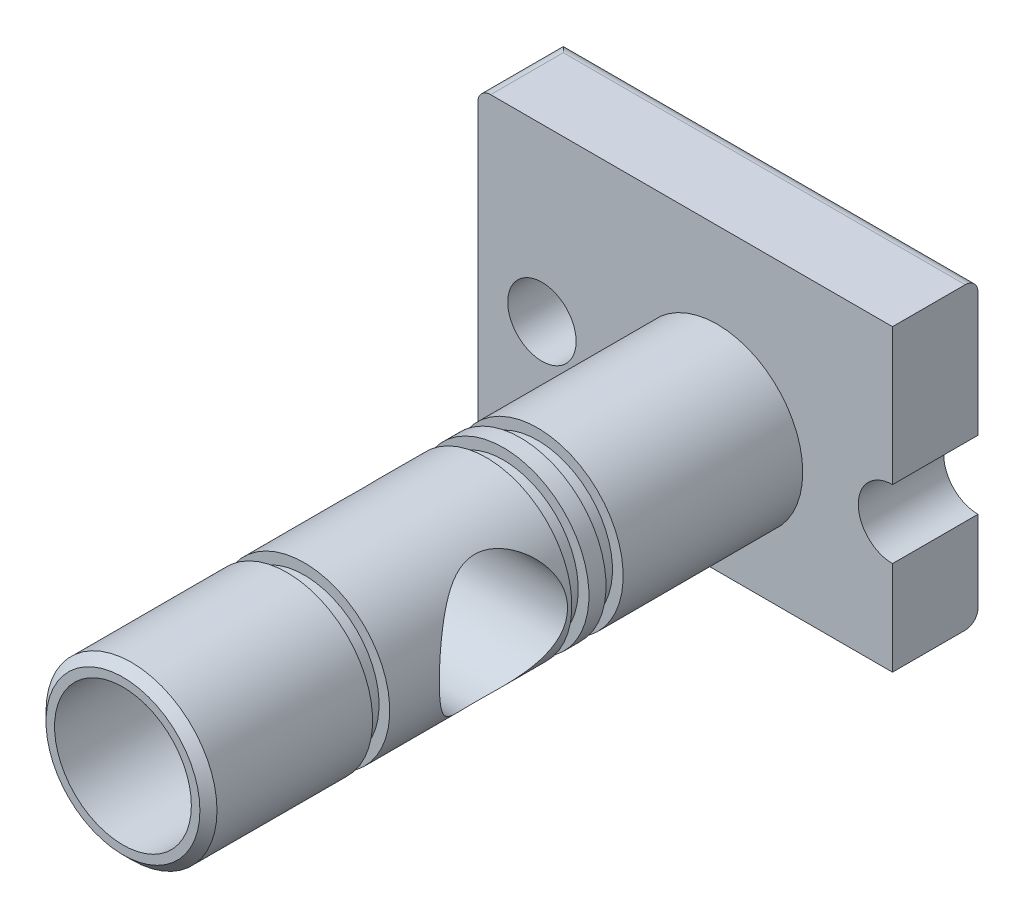
SolidWorks part; units mm, degrees
ref_plane "Front Plane" through (0, 0, 0) normal (0, 0, 1) x (1, 0, 0)
ref_plane "Top Plane" through (0, 0, 0) normal (0, 1, 0) x (1, 0, 0)
ref_plane "Right Plane" through (0, 0, 0) normal (1, 0, 0) x (0, 0, -1)
sketch "Sketch1" plane through (0, 0, 0) normal (0, 0, 1) x (1, 0, 0)
  line L1 (-56, 40) -> (41, 40)
  line L3 (-56, -30) -> (41, -30)
  line L4 (41, 40) -> (41, 8)
  line L5 (41, -8) -> (41, -30)
  line L6 (-56, 40) -> (-56, -30)
  arc A1 (41, 8) -> (41, -8) centre (41, 0) ccw
  circle A2 centre (-41, 0) radius 8
  dimension "D5" = 56
  dimension "D6" = 16
  dimension "D1" = 70
  dimension "D2" = 97
  dimension "D3" = 15
  dimension "D4" = 30
extrude "Boss-Extrude1" add sketch "Sketch1" along normal blind 20
sketch "Sketch2" plane through (0, 0, 20) normal (0, 0, 1) x (1, 0, 0)
  circle A0 centre (0, 0) radius 20
  dimension "D1" = 40
extrude "Boss-Extrude2" add sketch "Sketch2" along normal blind 139
sketch "Sketch3" plane through (0, 0, 0) normal (1, 0, 0) x (0, 0, -1)
  line L0 (-20, 8) -> (-20, 40) construction
  circle A0 centre (-90, 0) radius 15
  point P4 (0, 0)
  dimension "D1" = 30
  dimension "D2" = 70
extrude "Cut-Extrude1" cut sketch "Sketch3" against normal through all both and the other way through all
sketch "Sketch4" plane through (0, 0, 0) normal (1, 0, 0) x (0, 0, -1)
  line L0 (-20, 20) -> (-159, 20) construction
  line L1 (-66, 20) -> (-62, 20)
  line L2 (-66, 20) -> (-66, 17.5)
  line L3 (-66, 17.5) -> (-62, 17.5)
  line L4 (-62, 20) -> (-62, 17.5)
  line L5 (-20, 8) -> (-20, 40) construction
  line L6 (-74, 20) -> (-70, 20)
  line L7 (-74, 20) -> (-74, 17.5)
  line L8 (-74, 17.5) -> (-70, 17.5)
  line L9 (-70, 20) -> (-70, 17.5)
  line L10 (-120.6, 20) -> (-116.6, 20)
  line L11 (-120.6, 20) -> (-120.6, 17.5)
  line L12 (-120.6, 17.5) -> (-116.6, 17.5)
  line L13 (-116.6, 20) -> (-116.6, 17.5)
  line L14 (0, 0) -> (-203.4126, 0) construction
  dimension "D1" = 2.5
  dimension "D2" = 4
  dimension "D3" = 4
  dimension "D4" = 4
  dimension "D5" = 4
  dimension "D6" = 42
  dimension "D7" = 42.6
revolve "Cut-Revolve1" cut sketch "Sketch4" angle 360 about L14
sketch "Sketch5" plane through (0, 0, 159) normal (0, 0, 1) x (1, 0, 0)
  circle A0 centre (0, 0) radius 16
  dimension "D1" = 32
extrude "Cut-Extrude2" cut sketch "Sketch5" against normal blind 35.4
sketch "Sketch6" plane through (0, 0, 123.6) normal (0, 0, 1) x (1, 0, 0)
  circle A0 centre (0, 0) radius 9.5
  dimension "D1" = 19
extrude "Cut-Extrude3" cut sketch "Sketch6" against normal blind 22
chamfer "Chamfer1" distance 2 1 edges at (20, 0, 159)
fillet "Fillet1" radius 3 4 edges at (-7.5, -30, 0) (-7.5, 40, 0) (-56, -30, 10) (-56, 40, 10)
